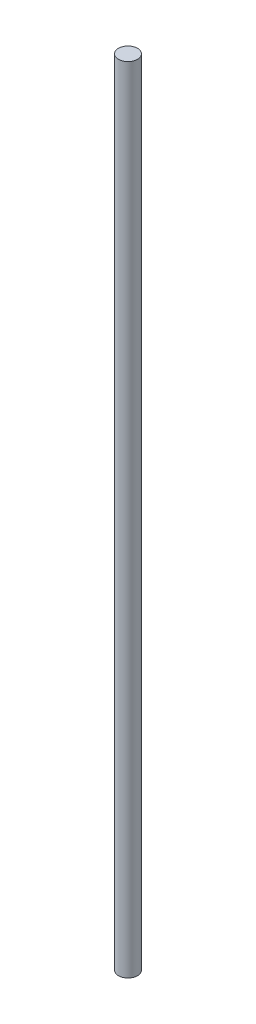
SolidWorks part; units mm, degrees
ref_plane "Front Plane" through (0, 0, 0) normal (0, 0, 1) x (1, 0, 0)
ref_plane "Top Plane" through (0, 0, 0) normal (0, 1, 0) x (1, 0, 0)
ref_plane "Right Plane" through (0, 0, 0) normal (1, 0, 0) x (0, 0, -1)
sketch "Sketch1" plane through (0, 0, 0) normal (0, 1, 0) x (1, 0, 0)
  circle A0 centre (0, 0) radius 4
  dimension "D1" = 8
  dimension "D2" = 0
  dimension "D3" = 0
extrude "Boss-Extrude1" add sketch "Sketch1" along normal blind 332.5
